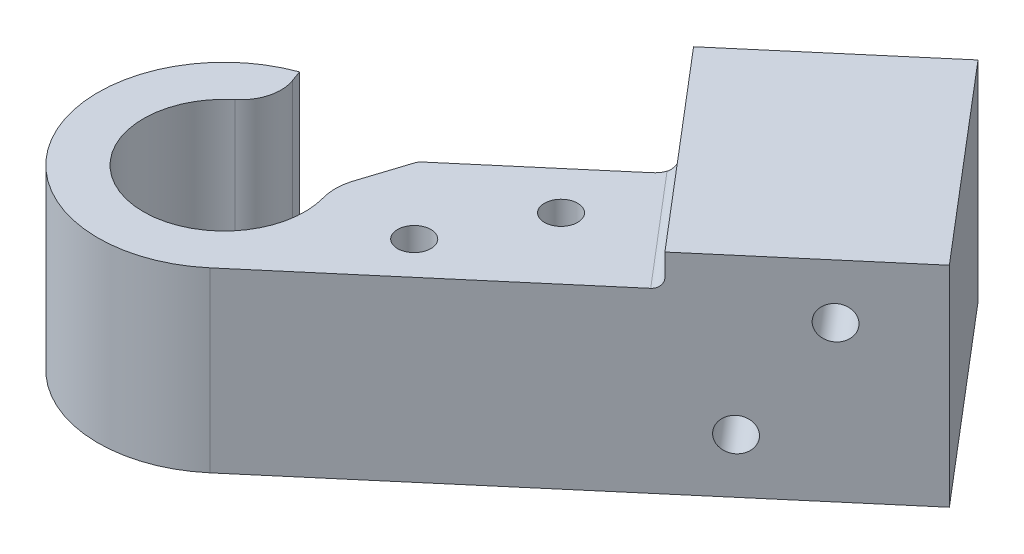
SolidWorks part; units mm, degrees
material "6061-T6 (SS)"
ref_plane "Front Plane" through (0, 0, 0) normal (0, 0, 1) x (1, 0, 0)
ref_plane "Top Plane" through (0, 0, 0) normal (0, 1, 0) x (1, 0, 0)
ref_plane "Right Plane" through (0, 0, 0) normal (1, 0, 0) x (0, 0, -1)
sketch "Sketch1" plane through (0, 0, 0) normal (0, 1, 0) x (1, 0, 0)
  circle A0 centre (0, 0) radius 12.5
  dimension "D2" = 25
extrude "Boss-Extrude1" add sketch "Sketch1" along normal blind 17.6
sketch "Sketch2" plane through (0, 17.6, 0) normal (0, 1, 0) x (1, 0, 0)
  circle A0 centre (0, 0) radius 6.875
  dimension "D1" = 13.75
extrude "Cut-Extrude1" cut sketch "Sketch2" against normal blind 50.8
sketch "Sketch3" plane through (0, 17.6, 0) normal (0, 1, 0) x (1, 0, 0)
  circle A0 centre (0, 0) radius 8
  dimension "D1" = 16
extrude "Cut-Extrude3" cut sketch "Sketch3" against normal offset from surface (15.6 mm away) 2 up to face at (0, 0, 6.875)
sketch "Sketch4" plane through (0, 17.6, 0) normal (0, 1, 0) x (1, 0, 0)
  line L0 (0, 0) -> (18.2932, 12.809)
  line L1 (0, 0) -> (-8.7404, 24.0142)
  line L2 (0, 0) -> (0, 22.9529) construction
  line L3 (0, 0) -> (-17.2058, 0) construction
  circle A0 centre (0, 0) radius 8 construction
  circle A1 centre (0, 0) radius 12.5 construction
  circle A2 centre (0, 0) radius 8
  circle A3 centre (0, 0) radius 12.5
  circle M3 centre (0, 0) radius 8
  circle M4 centre (0, 0) radius 12.5
  dimension "D1" = 75
  dimension "D2" = 55
extrude "Cut-Extrude4" cut sketch "Sketch4" against normal through all contours L1 L0 M3 M4
sketch "Sketch5" plane through (0, 17.6, 0) normal (0, 1, 0) x (1, 0, 0)
  line L0 (32.4721, 11.2168) -> (23.3996, 21.8794)
  line L1 (8.1004, -9.5202) -> (32.4721, 11.2168)
  line L4 (23.3996, 21.8794) -> (10.7177, 11.0888)
  line L5 (10.7177, 11.0888) -> (10.2394, 7.1697)
  arc A0 (-4.2753, 11.7462) -> (10.2394, 7.1697) centre (0, 0) ccw construction
  arc A1 (-4.8741, 11.5106) -> (10.2394, 7.1697) centre (0, 0) ccw
  dimension "D1" = 32
extrude "Boss-Extrude2" add sketch "Sketch5" against normal through all
fillet "Fillet1" radius 4 1 edges at (-2.7362, 9.8, -7.5175)
sketch "Sketch6" plane through (24.3717, 0, -20.737) normal (0.7616, 0, -0.648) x (-0.648, 0, -0.7616)
  line L1 (-12.5, 0) -> (12.5, 0)
  line L2 (-12.5, 0) -> (-12.5, 20.775)
  line L3 (-12.5, 20.775) -> (12.5, 20.775)
  line L4 (12.5, 0) -> (12.5, 20.775)
  point P4 (0, 0)
  dimension "D2" = 25
extrude "Boss-Extrude3" add sketch "Sketch6" along normal blind 20
hole_wizard "M4x0.7 Tapped Hole2" positions "Sketch7" profile "Sketch9" tap size "M4x0.7" standard "ANSI Metric"
sketch "Sketch7" plane through (-8.1004, 0, -9.5202) normal (-0.648, 0, -0.7616) x (-0.7616, 0, 0.648)
  line L0 (-44, 15.3875) -> (-37, 5.3875) construction
  line L2 (-32, 0) -> (-32, 20.775) construction
  line L3 (-52, 10.3875) -> (-28.7744, 10.3875) construction
  line L4 (-52, 0) -> (-52, 20.775) construction
  point P0 (-44, 15.3875)
  point P2 (-37, 5.3875)
  point P18 (-40.5, 10.3875)
  dimension "D1" = 7
  dimension "D2" = 10
  dimension "D3" = 5
sketch "Sketch9" plane through (25.4107, 15.3875, -38.0335) normal (0, 1, 0) x (-0.7616, 0, 0.648)
  line L0 (0, 0) -> (0, 7.9914)
  line L1 (0, 7.9914) -> (1.65, 7)
  line L2 (1.65, 7) -> (1.65, 0)
  line L5 (1.65, 0) -> (0, 0)
  line L10 (0, 7.9914) -> (-1.65, 7) construction
  line L11 (0, -6.35) -> (0, 107.95) construction
  dimension "Tap Drill Dia." = 3.3
  dimension "Tap Drill Depth" = 7
  dimension "Drill Angle" = 118
ref_plane "Plane1" through (0, 0, 0) normal (-0.648, 0, -0.7616) x (-0.7616, 0, 0.648)
mirror "Mirror1" about plane through (0, 0, 0) normal (-0.648, 0, -0.7616) of "M4x0.7 Tapped Hole2"
hole_wizard "M4x0.7 Tapped Hole1" positions "Sketch10" profile "Sketch11" tap size "M4x0.7" standard "ANSI Metric"
sketch "Sketch10" plane through (0, 17.6, 0) normal (0, 1, 0) x (1, 0, 0)
  line L5 (20.785, 12.6072) -> (13.1689, 6.1269)
  line L6 (13.1689, 6.1269) -> (15.761, 3.0804)
  line L7 (15.761, 3.0804) -> (20.785, 12.6072)
  line L9 (8.1004, -9.5202) -> (32.4721, 11.2168) construction
  line L11 (16.2713, 30.2571) -> (32.4721, 11.2168) construction
  point P0 (20.785, 12.6072)
  point P2 (15.761, 3.0804)
  dimension "D1" = 8.6325
  dimension "D2" = 10
  dimension "D3" = 4
  dimension "D4" = 8
sketch "Sketch11" plane through (20.785, 17.6, -12.6072) normal (1, 0, 0) x (0, 0, 1)
  line L0 (0, 0) -> (0, 7.9914)
  line L1 (0, 7.9914) -> (1.65, 7)
  line L2 (1.65, 7) -> (1.65, 0)
  line L5 (1.65, 0) -> (0, 0)
  line L10 (0, 7.9914) -> (-1.65, 7) construction
  line L11 (0, -6.35) -> (0, 107.95) construction
  dimension "Tap Drill Dia." = 3.3
  dimension "Tap Drill Depth" = 7
  dimension "Drill Angle" = 118
cosmetic thread "Hole Thread1" parameters "D1"=7, "D2"=4
cosmetic thread "Hole Thread2" parameters "D1"=7, "D2"=4
fillet "Fillet4" radius 1 1 edges at (27.9358, 17.6, -16.5481)
fillet "Fillet6" radius 1 2 edges at (-2.7362, 1, -7.5175) (6.5532, 1, -4.5886)
fillet "Fillet7" radius 2 1 edges at (23.3996, 9.3, -21.8794)
sketch "Sketch13" plane through (0, 17.6, 0) normal (0, 1, 0) x (1, 0, 0)
  line L0 (7.2378, 3.4079) -> (11.3366, 16.1604)
  line L2 (7.2378, 3.4079) -> (6.3488, 4.8675)
  line L3 (6.3488, 4.8675) -> (5.1423, 6.1284)
  line L6 (10.7177, 11.0888) -> (10.2394, 7.1697) construction
  line L7 (11.3366, 16.1604) -> (5.1423, 6.1284)
  arc A0 (-5.0855, 6.1756) -> (6.5532, 4.5886) centre (0, 0) ccw construction
extrude "Cut-Extrude6" cut sketch "Sketch13" against normal up to surface (15.6 mm away) up to face at (0.7248, 2, -5.0161)
fillet "Fillet8" radius 5 1 edges at (7.2378, 9.8, -3.4079)
sketch "Sketch14" plane through (0, 17.6, 0) normal (0, 1, 0) x (1, 0, 0)
  line L0 (7.9264, 5.5501) -> (9.3259, 9.9046)
  line L1 (7.7595, 5.031) -> (7.9264, 5.5501) construction
  line L2 (7.9264, 5.5501) -> (10.2394, 7.1697) construction
  line L4 (10.7177, 11.0888) -> (10.2394, 7.1697) construction
  line L5 (10.2394, 7.1697) -> (7.9264, 5.5501)
  line L6 (10.2394, 7.1697) -> (10.7177, 11.0888)
  line L7 (21.8764, 20.5833) -> (10.7177, 11.0888) construction
  line L8 (10.7177, 11.0888) -> (9.3259, 9.9046)
extrude "Boss-Extrude4" add sketch "Sketch14" against normal up to vertex (17.6 mm away)
fillet "Fillet11" radius 1 1 edges at (9.3259, 8.8, -9.9046)
equation "\"1.1c\"=0.0104601"
